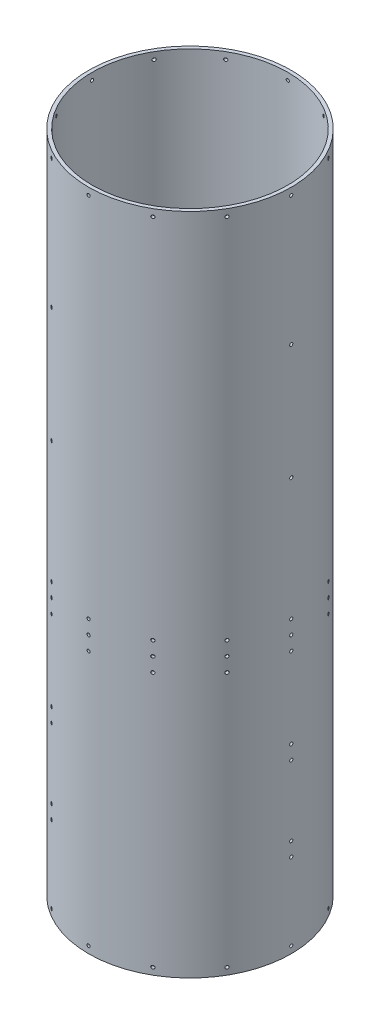
SolidWorks part; units mm, degrees
material "Acrylic (Medium-high impact)"
ref_plane "Front Plane" through (0, 0, 0) normal (0, 0, 1) x (1, 0, 0)
ref_plane "Top Plane" through (0, 0, 0) normal (0, 1, 0) x (1, 0, 0)
ref_plane "Right Plane" through (0, 0, 0) normal (1, 0, 0) x (0, 0, -1)
sketch "Sketch1" plane through (0, 0, 0) normal (0, 1, 0) x (1, 0, 0)
  circle A0 centre (0, 0) radius 92.075
  circle A1 centre (0, 0) radius 88.9
  dimension "D1" = 184.15
  dimension "D2" = 177.8
extrude "Boss-Extrude1" add sketch "Sketch1" along normal mid plane 603.25
ref_plane "Plane1" through (92.075, 0, 0) normal (1, 0, 0) x (0, 0, -1)
sketch "Sketch3" plane through (92.075, 0, 0) normal (1, 0, 0) x (0, 0, -1)
  line L0 (0, 101.2825) -> (0, -101.2825) construction
  line L1 (88.9, 301.625) -> (-88.9, 301.625) construction
  line L2 (-92.075, -301.625) -> (92.075, -301.625) construction
  circle A0 centre (0, -295.275) radius 1.4351
  circle A1 centre (0, 295.275) radius 1.4351
  circle A2 centre (0, -63.373) radius 1.4351
  circle A3 centre (0, -50.673) radius 1.4351
  circle A4 centre (0, -37.973) radius 1.4351
  dimension "D1" = 6.35
  dimension "D2" = 2.8702
  dimension "D3" = 2.8702
  dimension "D4" = 6.35
  dimension "D5" = 231.902
  dimension "D6" = 2.8702
  dimension "D7" = 2.8702
  dimension "D8" = 2.8702
  dimension "D9" = 12.7
  dimension "D10" = 12.7
extrude "Cut-Extrude1" cut sketch "Sketch3" against normal blind 34.798
pattern_circular "CirPattern1" count 12 over 360 about axis through (0, 301.625, 0) along (0, -1, 0) of "Cut-Extrude1"
sketch "Sketch4" plane through (92.075, 0, 0) normal (1, 0, 0) x (0, 0, -1)
  line L0 (0, 101.2825) -> (0, -101.2825) construction
  circle A0 centre (0, -225.425) radius 1.4351
  circle A1 centre (0, -295.275) radius 1.4351 construction
  circle A2 centre (0, -212.725) radius 1.4351
  circle A3 centre (0, -149.225) radius 1.4351
  circle A4 centre (0, -136.525) radius 1.4351
  circle A5 centre (0, 177.927) radius 1.4351
  circle A6 centre (0, 295.275) radius 1.4351 construction
  circle A7 centre (0, 73.025) radius 1.4351
  dimension "D1" = 69.85
  dimension "D3" = 2.8702
  dimension "D4" = 2.8702
  dimension "D6" = 2.8702
  dimension "D7" = 2.8702
  dimension "D8" = 12.7
  dimension "D9" = 117.348
  dimension "D10" = 2.8702
  dimension "D11" = 104.902
  dimension "D12" = 2.8702
  dimension "D2" = 12.7
  dimension "D5" = 63.5
extrude "Cut-Extrude2" cut sketch "Sketch4" against normal blind 55.372
pattern_circular "CirPattern2" count 3 over 360 about axis through (0, 301.625, 0) along (0, -1, 0) of "Cut-Extrude2"
